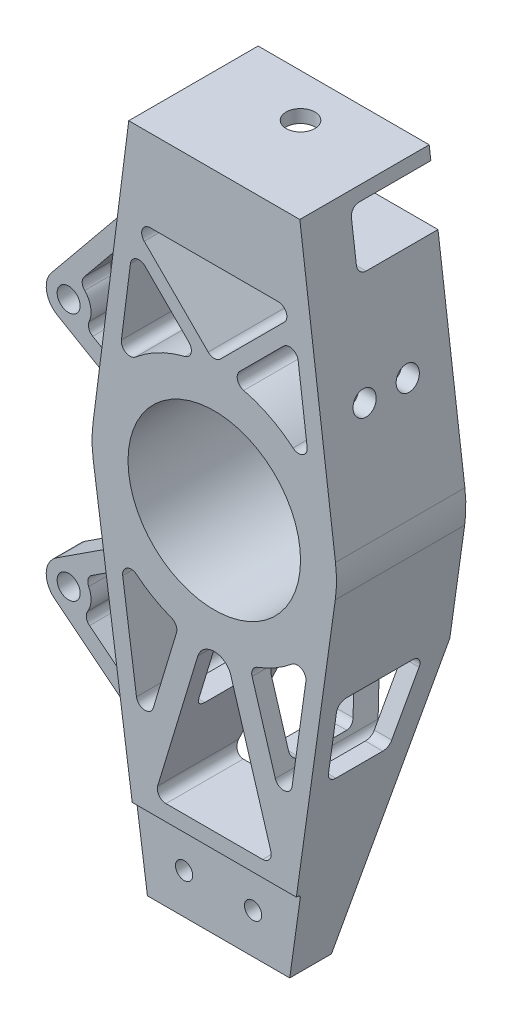
SolidWorks part; units mm, degrees
ref_plane "Front Plane" through (0, 0, 0) normal (0, 0, 1) x (1, 0, 0)
ref_plane "Top Plane" through (0, 0, 0) normal (0, 1, 0) x (1, 0, 0)
ref_plane "Right Plane" through (0, 0, 0) normal (1, 0, 0) x (0, 0, -1)
sketch "Sketch1" plane through (0, 0, 0) normal (0, 0, 1) x (1, 0, 0)
  line L0 (-29.75, 102.5) -> (-42.1573, 5.386)
  line L1 (-29.75, 102.5) -> (29.75, 102.5)
  line L3 (-24.75, -129.2275) -> (24.75, -129.2275)
  line L5 (0, 185.9794) -> (0, -218.2412) construction
  line L6 (29.75, 102.5) -> (42.1573, 5.386)
  line L7 (-30.3249, 98) -> (30.3249, 98) construction
  line L8 (-24.75, -129.2275) -> (-30.1796, -90.6073)
  line L9 (24.75, -129.2275) -> (42.0861, -5.9168)
  line L10 (-31.858, -35.5713) -> (-27.0621, -69.6844)
  line L11 (31.858, -35.5713) -> (27.0621, -69.6844)
  line L12 (-29.1615, 59.7616) -> (-32.3037, 35.167)
  line L13 (29.1615, 59.7616) -> (32.3037, 35.167)
  line L14 (-32.8163, 78.5) -> (32.8163, 78.5) construction
  line L15 (-22.2479, 74) -> (22.2479, 74)
  line L16 (-24.3693, 68.8787) -> (-2.1213, 46.6307)
  line L17 (2.1213, 46.6307) -> (24.3693, 68.8787)
  line L18 (-24.0644, 61.5027) -> (-8.8423, 46.2807)
  line L19 (24.0644, 61.5027) -> (8.8423, 46.2807)
  line L20 (-21.2199, -70.1355) -> (-13.1477, -43.4556)
  line L21 (21.2199, -70.1355) -> (13.1477, -43.4556)
  line L22 (-16.8181, -96.7275) -> (16.8181, -96.7275)
  line L23 (19.6896, -92.8587) -> (5.7429, -46.7625)
  line L24 (-5.7429, -46.7625) -> (-19.6896, -92.8587)
  line L29 (-37.8367, -36.1429) -> (-42.0861, -5.9168)
  line L30 (-30.1796, -90.6073) -> (-37.8367, -36.1429)
  line L31 (0.0039, -42.5) -> (132.5634, -42.5868) construction
  line L32 (-0.0039, -42.5) -> (-132.5634, -42.5868) construction
  arc A0 (-42.1573, 5.386) -> (-42.0861, -5.9168) centre (0, 0) ccw
  circle A1 centre (0, 0) radius 30
  arc A2 (22.2479, 74) -> (24.3693, 68.8787) centre (22.2479, 71) cw
  arc A3 (-22.2479, 74) -> (-24.3693, 68.8787) centre (-22.2479, 71) ccw
  arc A4 (29.1615, 59.7616) -> (24.0644, 61.5027) centre (26.1857, 59.3814) ccw
  arc A5 (-29.1615, 59.7616) -> (-24.0644, 61.5027) centre (-26.1857, 59.3814) cw
  arc A6 (27.3942, 32.4932) -> (10.2408, 41.2477) centre (0, 0) ccw
  arc A7 (-32.3037, 35.167) -> (-27.3942, 32.4932) centre (-29.3279, 34.7868) ccw
  arc A8 (32.3037, 35.167) -> (27.3942, 32.4932) centre (29.3279, 34.7868) cw
  arc A9 (-10.2408, 41.2477) -> (-27.3942, 32.4932) centre (0, 0) ccw
  arc A10 (-2.1213, 46.6307) -> (2.1213, 46.6307) centre (0, 48.7521) ccw
  arc A11 (8.8423, 46.2807) -> (10.2408, 41.2477) centre (10.9636, 44.1594) ccw
  arc A12 (-8.8423, 46.2807) -> (-10.2408, 41.2477) centre (-10.9636, 44.1594) cw
  arc A13 (5.7429, -46.7625) -> (-5.7429, -46.7625) centre (0, -48.5) ccw
  arc A14 (27.0621, -69.6844) -> (21.2199, -70.1355) centre (24.0913, -69.2667) cw
  arc A15 (-27.0621, -69.6844) -> (-21.2199, -70.1355) centre (-24.0913, -69.2667) ccw
  arc A16 (-26.9826, -32.8358) -> (-14.963, -39.7789) centre (0, 0) ccw
  arc A17 (42.0861, -5.9168) -> (42.1573, 5.386) centre (0, 0) ccw
  arc A18 (31.858, -35.5713) -> (26.9826, -32.8358) centre (28.8872, -35.1536) ccw
  arc A19 (-31.858, -35.5713) -> (-26.9826, -32.8358) centre (-28.8872, -35.1536) cw
  arc A20 (14.963, -39.7789) -> (26.9826, -32.8358) centre (0, 0) ccw
  arc A21 (13.1477, -43.4556) -> (14.963, -39.7789) centre (16.0192, -42.5868) cw
  arc A22 (-13.1477, -43.4556) -> (-14.963, -39.7789) centre (-16.0192, -42.5868) ccw
  arc A23 (16.8181, -96.7275) -> (19.6896, -92.8587) centre (16.8181, -93.7275) ccw
  arc A24 (-16.8181, -96.7275) -> (-19.6896, -92.8587) centre (-16.8181, -93.7275) cw
  circle A32 centre (-12, -115.2275) radius 3
  circle A33 centre (12, -115.2275) radius 3
  point P8 (0, 102.5)
  point P17 (0, -129.2275)
  point P34 (0, 74)
  point P45 (28.3868, 65.8252)
  point P48 (-28.3868, 65.8252)
  point P50 (-33.4466, 26.2217)
  point P53 (33.4466, 26.2217)
  point P56 (0, 44.5094)
  point P59 (4.7908, 42.2291)
  point P62 (-4.7908, 42.2291)
  point P65 (0, -27.7811)
  point P68 (25.1653, -83.176)
  point P71 (-25.1653, -83.176)
  point P74 (33.1135, -26.641)
  point P77 (-33.1135, -26.641)
  point P80 (12.3076, -40.6789)
  point P83 (-12.3076, -40.6789)
  point P85 (-36.9395, -42.5242)
  point P90 (-30.1796, -90.6073)
  point P98 (0, -30)
  point P105 (-30.9547, -85.0941)
  point P108 (-33.4499, 73.5403)
  dimension "D1" = 85
  dimension "D2" = 60
  dimension "D13" = 3
  dimension "D14" = 3
  dimension "D15" = 3
  dimension "D16" = 3
  dimension "D17" = 3
  dimension "D19" = 6
  dimension "D20" = 3
  dimension "D21" = 3
  dimension "D22" = 3
  dimension "D24" = 3
  dimension "D25" = 46.0963
  dimension "D28" = 6
  dimension "D30" = 24
  dimension "D3" = 102.5
  dimension "D4" = 59.5
  dimension "D5" = 4.5
  dimension "D6" = 49.5
  dimension "D7" = 123.3107
  dimension "D8" = 6
  dimension "D9" = 6
  dimension "D10" = 19.5
  dimension "D11" = 4.5
  dimension "D12" = 5
  dimension "D18" = 15.2221
  dimension "D23" = 32.5
  dimension "D26" = 39
  dimension "D27" = 55
  dimension "D29" = 14
  dimension "D35" = 5
extrude "Boss-Extrude1" add sketch "Sketch1" along normal mid plane 45
sketch "Sketch2" plane through (0, 0, 22.5) normal (0, 0, 1) x (1, 0, 0)
  line L0 (-24.75, -129.2275) -> (24.75, -129.2275) construction
  line L1 (-21.75, -101.2275) -> (21.75, -101.2275)
  line L2 (-21.75, -101.2275) -> (-21.75, -129.2275)
  line L3 (-21.75, -129.2275) -> (21.75, -129.2275)
  line L4 (21.75, -101.2275) -> (21.75, -129.2275)
  line L5 (0, 185.9794) -> (0, -218.2412) construction
  line L6 (-16.8181, -96.7275) -> (16.8181, -96.7275) construction
  point P6 (0, -129.2275)
  dimension "D3" = 28
  dimension "D1" = 43.5
  dimension "D2" = 4.5
extrude "Cut-Extrude1" cut sketch "Sketch2" against normal blind 45 from offset 6.7
sketch "Sketch6" plane through (0, 0, 0) normal (1, 0, 0) x (0, 0, -1)
  line L0 (22.5, -5.9168) -> (22.5, -129.2275) construction
  line L1 (22.5, -102.2275) -> (22, -102.2275)
  line L2 (22.5, -102.2275) -> (22.5, -129.2275)
  line L3 (22.5, -129.2275) -> (21, -129.2275)
  line L4 (21, -103.2275) -> (21, -129.2275)
  line L5 (-22.5, -129.2275) -> (22.5, -129.2275) construction
  line L6 (21, -129.2275) -> (6.5, -129.2275) construction
  line L7 (6.5, -129.2275) -> (-22.5, -42.5242)
  line L8 (-22.5, -5.9168) -> (-22.5, -129.2275) construction
  line L9 (-22.5, -42.5242) -> (-22.5, -129.2275)
  line L10 (-22.5, -101.2275) -> (-22.5, -129.2275) construction
  line L11 (-22.5, -129.2275) -> (6.5, -129.2275)
  line L12 (-22.5, 98) -> (2.5, 98)
  line L13 (-22.5, 5.386) -> (-22.5, 102.5) construction
  line L14 (5.5, 95) -> (5.5, 81.5)
  line L15 (-22.5, 78.5) -> (2.5, 78.5)
  line L16 (-22.5, 78.5) -> (-22.5, 98)
  line L17 (-22.5, 102.5) -> (22.5, 102.5) construction
  arc A1 (5.5, 81.5) -> (2.5, 78.5) centre (2.5, 81.5) cw
  arc A2 (2.5, 98) -> (5.5, 95) centre (2.5, 95) cw
  arc A3 (22, -102.2275) -> (21, -103.2275) centre (22, -103.2275) ccw
  point P10 (22.5, -102.2275)
  point P28 (5.5, 78.5)
  point P31 (5.5, 98)
  dimension "D3" = 1
  dimension "D10" = 3
  dimension "D1" = 1.5
  dimension "D2" = 27
  dimension "D4" = 14.5
  dimension "D5" = 86.7033
  dimension "D6" = 4.5
  dimension "D7" = 28
  dimension "D8" = 28
  dimension "D9" = 19.5
extrude "Cut-Extrude3" cut sketch "Sketch6" against normal through all both and the other way through all
sketch "Sketch7" plane through (0, 102.5, 0) normal (0, 1, 0) x (1, 0, 0)
  line L0 (-21.75, -22.5) -> (21.75, -22.5) construction
  circle A0 centre (0, -7.5) radius 5
  dimension "D1" = 10
  dimension "D2" = 15
extrude "Cut-Extrude4" cut sketch "Sketch7" against normal up to surface (28.5 mm away) up to face at (0, 74, 0)
sketch "Sketch8" plane through (0, 0, 0) normal (1, 0, 0) x (0, 0, -1)
  line L0 (-9.5, -42.5242) -> (13.5, -42.5242)
  line L1 (16.5, -45.5242) -> (16.5, -65.5242)
  line L2 (13.5, -68.5242) -> (-2.8105, -68.5242)
  line L3 (-5.6556, -66.4758) -> (-12.3451, -46.4758)
  line L4 (22.5, -102.2275) -> (22.5, -5.9168) construction
  line L5 (-22.5, -42.5242) -> (6.5, -129.2275) construction
  arc A0 (-2.8105, -68.5242) -> (-5.6556, -66.4758) centre (-2.8105, -65.5242) cw
  arc A1 (16.5, -65.5242) -> (13.5, -68.5242) centre (13.5, -65.5242) cw
  arc A2 (13.5, -42.5242) -> (16.5, -45.5242) centre (13.5, -45.5242) cw
  arc A3 (-9.5, -42.5242) -> (-12.3451, -46.4758) centre (-9.5, -45.5242) ccw
  dimension "D1" = 3
  dimension "D2" = 23
  dimension "D3" = 20
  dimension "D4" = 6
extrude "Cut-Extrude5" cut sketch "Sketch8" against normal up to surface and the other way through all up to face at (-29.7442, -50.6071, 2.6831)
sketch "Sketch10" plane through (0, 0, 0) normal (1, 0, 0) x (0, 0, -1)
  line L0 (-7.5, 43.5) -> (7.5, 43.5) construction
  line L1 (2.5, 78.5) -> (-22.5, 78.5) construction
  circle A0 centre (-7.5, 43.5) radius 4
  circle A1 centre (-7.5, 43.5) radius 4
  circle A2 centre (7.5, 43.5) radius 4
  point P8 (0, 43.5)
  dimension "D1" = 8
  dimension "D2" = 15
  dimension "D3" = 35
extrude "Cut-Extrude6" cut sketch "Sketch10" along normal through all from surface contours A2 | A0
ref_plane "Plane1" through (0, 0, -4.1) normal (0, 0, 1) x (1, 0, 0)
sketch "Sketch12" plane through (0, 0, -4.1) normal (0, 0, 1) x (1, 0, 0)
  line L0 (-30.1796, -90.6073) -> (-37.8367, -36.1429) construction
  line L1 (-30.3188, -89.617) -> (-63.9208, -62.786)
  line L2 (-38.168, -33.7861) -> (-63.3094, -50.154)
  line L3 (-59.0538, -84.6382) -> (-59.0538, 139.5785) construction
  line L4 (-37.8367, -36.1429) -> (-42.0861, -5.9168) construction
  line L5 (-29.75, 102.5) -> (-42.1573, 5.386) construction
  line L6 (-38.168, -33.7861) -> (-36.5057, -45.6102)
  line L10 (-32.3586, -75.1083) -> (-30.3188, -89.617)
  line L11 (-51.041, -49.3263) -> (-41.1344, -42.8768)
  line L12 (-51.7896, -64.7946) -> (-37.0867, -76.5348)
  line L13 (0, 185.9794) -> (0, -218.2412) construction
  line L14 (-33.4551, 73.5) -> (-65.0936, 34.7831)
  line L15 (-41.4898, 10.6112) -> (-62.9747, 23.1046)
  line L16 (-53.656, 39.2975) -> (-41.5168, 54.1525)
  line L18 (-44.5749, 19.3459) -> (-50.6802, 22.896)
  line L19 (-33.4551, 73.5) -> (-36.218, 51.874)
  line L20 (-41.4898, 10.6112) -> (-40.0911, 21.5591)
  arc A0 (-63.3094, -50.154) -> (-63.9208, -62.786) centre (-59.0538, -56.6908) ccw
  arc A1 (-65.0936, 34.7831) -> (-62.9747, 23.1046) centre (-59.0538, 29.8475) ccw
  arc A3 (-41.1344, -42.8768) -> (-36.5057, -45.6102) centre (-39.4977, -45.391) cw
  arc A4 (-37.0867, -76.5348) -> (-32.3586, -75.1083) centre (-35.2147, -74.1905) ccw
  circle A5 centre (-59.0538, -56.6908) radius 7.8 construction
  arc A6 (-52.0846, -53.1878) -> (-52.4555, -60.8504) centre (-59.0538, -56.6908) cw
  arc A7 (-51.7896, -64.7946) -> (-52.4555, -60.8504) centre (-49.9177, -62.4503) cw
  arc A8 (-51.041, -49.3263) -> (-52.0846, -53.1878) centre (-49.4042, -51.8405) ccw
  circle A9 centre (-59.0538, -56.6908) radius 4
  arc A10 (-51.917, 26.7) -> (-53.4776, 35.3015) centre (-59.0538, 29.8475) ccw
  arc A11 (-59.0538, 37.6475) -> (-59.0538, 22.0475) centre (-59.0538, 29.8475) ccw construction
  arc A12 (-50.6802, 22.896) -> (-51.917, 26.7) centre (-49.1721, 25.4894) cw
  arc A13 (-53.656, 39.2975) -> (-53.4776, 35.3015) centre (-51.333, 37.3992) ccw
  arc A14 (-40.0911, 21.5591) -> (-44.5749, 19.3459) centre (-43.0669, 21.9393) cw
  arc A15 (-41.5168, 54.1525) -> (-36.218, 51.874) centre (-39.1938, 52.2542) cw
  circle A16 centre (-59.0538, 29.8475) radius 4
  point P0 (-30.3188, -89.617)
  point P1 (-38.168, -33.7861)
  point P6 (-24.75, -129.2275)
  point P12 (-33.4551, 73.5)
  point P15 (-41.4898, 10.6112)
  point P33 (-54.2462, -62.833)
  point P36 (-53.6755, -51.0415)
  point P42 (-52.2323, 16.8579)
  point P50 (-49.2743, 54.1415)
  point P61 (-40.6643, 17.0719)
  point P64 (-34.891, 62.2607)
  dimension "D4" = 40
  dimension "D5" = 15.6
  dimension "D6" = 56.38
  dimension "D9" = 3
  dimension "D10" = 3
  dimension "D11" = 3
  dimension "D13" = 8
  dimension "D19" = 3
  dimension "D20" = 3
  dimension "D21" = 8
  dimension "D22" = 3
  dimension "D2" = 43
  dimension "D3" = 30
  dimension "D7" = 6
  dimension "D8" = 6
  dimension "D12" = 59.0538
  dimension "D14" = 5
  dimension "D15" = 63.4
  dimension "D16" = 50
  dimension "D17" = 6
  dimension "D18" = 6
  dimension "D23" = 7.0624
extrude "Boss-Extrude2" add sketch "Sketch12" against normal blind 10 contours A8 L11 A3 L6 L2 A0 L1 L10 A4 L12 A7 A6 A9 | L16 A15 L19 L14 A1 L15 L20 A14 L18 A12 A10 A13 A16
mirror "Mirror1" about plane through (0, 0, 0) normal (0, 0, 1) of bodies 108
delete or keep bodies "Body-Delete/Keep 1" type keep bodies bodies 109
